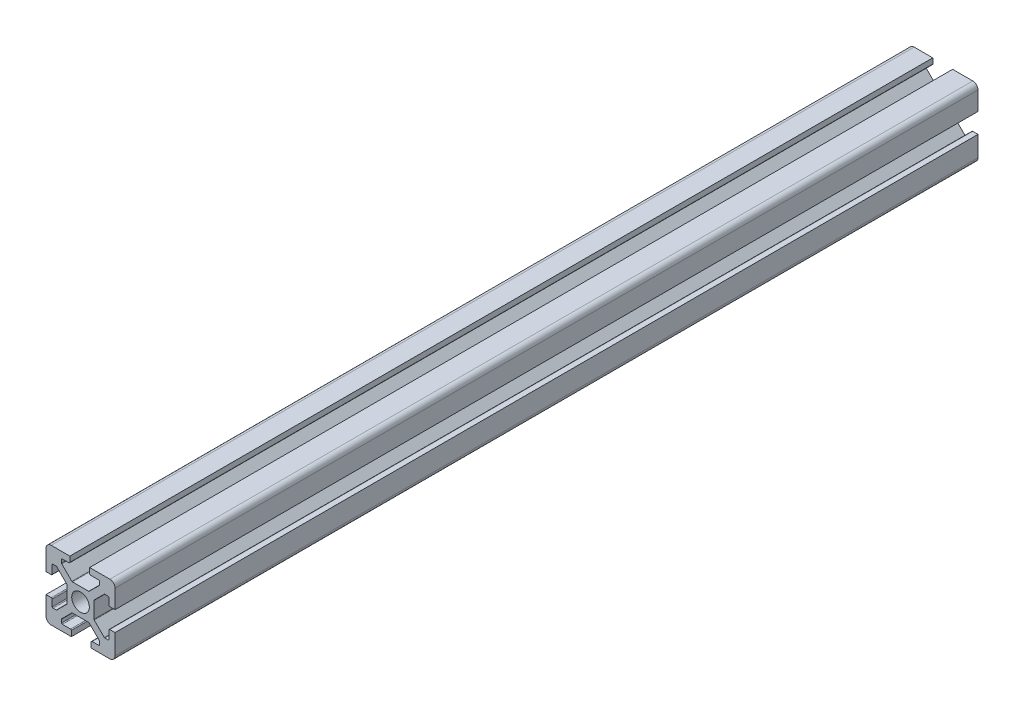
SolidWorks part; units mm, degrees
ref_plane "Front Plane" through (0, 0, 0) normal (0, 0, 1) x (1, 0, 0)
ref_plane "Top Plane" through (0, 0, 0) normal (0, 1, 0) x (1, 0, 0)
ref_plane "Right Plane" through (0, 0, 0) normal (1, 0, 0) x (0, 0, -1)
sketch "Sketch1" plane through (0, 0, 0) normal (0, 0, 1) x (1, 0, 0)
  line L1 (-8.5, -10) -> (-2.6476, -10)
  line L2 (-10, -8.5) -> (-10, -3.1)
  line L3 (-8.5, 10) -> (-3.1, 10)
  line L4 (10, -8.5) -> (10, -2.6476)
  line L5 (-1.8031, 1.8031) -> (1.8031, -1.8031) construction
  line L6 (-10, 10) -> (-3.9, 3.9) construction
  line L7 (2.3464, -3.9) -> (-2.3464, -3.9)
  line L8 (3.9, -2.3464) -> (3.9, 2.3464)
  line L9 (2.3464, 3.9) -> (-2.3464, 3.9)
  line L10 (-3.9, -2.3464) -> (-3.9, 2.3464)
  line L11 (1.8031, -1.8031) -> (-1.8031, 1.8031) construction
  line L12 (1.8031, 1.8031) -> (-1.8031, -1.8031) construction
  line L14 (-10, 2.6476) -> (-10, 8.5)
  line L15 (-10, 2.6476) -> (-8.45, 2.6476)
  line L17 (-10, -3.1) -> (-8.45, -3.1)
  line L18 (-3.9, 2.3464) -> (-3.9, -2.3464)
  line L19 (-8.2, 2.8976) -> (-8.2, 5.25)
  line L20 (-8.2, -3.35) -> (-8.2, -5.25)
  line L21 (-7.95, 5.5) -> (-7.0536, 5.5)
  line L22 (-6.8768, 5.4268) -> (-3.9732, 2.5232)
  line L23 (-6.8768, -5.4268) -> (-3.9732, -2.5232)
  line L24 (-7.95, -5.5) -> (-7.0536, -5.5)
  line L26 (-2.3464, 3.9) -> (2.3464, 3.9)
  line L27 (3.9, 3.9) -> (10, 10) construction
  line L28 (2.6476, 10) -> (2.6476, 8.45)
  line L29 (-3.1, 10) -> (-3.1, 8.45)
  line L30 (2.3464, 3.9) -> (-2.3464, 3.9)
  line L31 (2.8976, 8.2) -> (5.25, 8.2)
  line L32 (-3.35, 8.2) -> (-5.25, 8.2)
  line L33 (5.5, 7.95) -> (5.5, 7.0536)
  line L34 (5.4268, 6.8768) -> (2.5232, 3.9732)
  line L35 (-5.4268, 6.8768) -> (-2.5232, 3.9732)
  line L36 (-5.5, 7.95) -> (-5.5, 7.0536)
  line L37 (-1.8031, -1.8031) -> (1.8031, 1.8031) construction
  line L38 (3.9, 2.3464) -> (3.9, -2.3464)
  line L40 (10, -2.6476) -> (8.45, -2.6476)
  line L41 (10, 3.1) -> (8.45, 3.1)
  line L42 (3.9, -2.3464) -> (3.9, 2.3464)
  line L43 (8.2, -2.8976) -> (8.2, -5.25)
  line L44 (8.2, 3.35) -> (8.2, 5.25)
  line L45 (7.95, -5.5) -> (7.0536, -5.5)
  line L46 (6.8768, -5.4268) -> (3.9732, -2.5232)
  line L47 (6.8768, 5.4268) -> (3.9732, 2.5232)
  line L48 (7.95, 5.5) -> (7.0536, 5.5)
  line L50 (2.3464, -3.9) -> (-2.3464, -3.9)
  line L52 (-2.6476, -10) -> (-2.6476, -8.45)
  line L53 (3.1, -10) -> (3.1, -8.45)
  line L54 (-2.3464, -3.9) -> (2.3464, -3.9)
  line L55 (-2.8976, -8.2) -> (-5.25, -8.2)
  line L56 (3.35, -8.2) -> (5.25, -8.2)
  line L57 (-5.5, -7.95) -> (-5.5, -7.0536)
  line L58 (-5.4268, -6.8768) -> (-2.5232, -3.9732)
  line L59 (5.4268, -6.8768) -> (2.5232, -3.9732)
  line L60 (5.5, -7.95) -> (5.5, -7.0536)
  line L61 (2.6476, 10) -> (8.5, 10)
  line L62 (3.1, -10) -> (8.5, -10)
  line L63 (10, 3.1) -> (10, 8.5)
  line L65 (3.9, -3.9) -> (10, -10) construction
  circle A0 centre (0, 0) radius 2.55
  arc A1 (-8.2, -3.35) -> (-8.45, -3.1) centre (-8.45, -3.35) ccw
  arc A2 (-8.2, -5.25) -> (-7.95, -5.5) centre (-7.95, -5.25) ccw
  arc A3 (-6.8768, -5.4268) -> (-7.0536, -5.5) centre (-7.0536, -5.25) cw
  arc A4 (-3.9732, -2.5232) -> (-3.9, -2.3464) centre (-4.15, -2.3464) ccw
  arc A5 (-3.9, 2.3464) -> (-3.9732, 2.5232) centre (-4.15, 2.3464) ccw
  arc A6 (-7.0536, 5.5) -> (-6.8768, 5.4268) centre (-7.0536, 5.25) cw
  arc A7 (-8.2, 5.25) -> (-7.95, 5.5) centre (-7.95, 5.25) cw
  arc A8 (-8.2, 2.8976) -> (-8.45, 2.6476) centre (-8.45, 2.8976) cw
  arc A9 (-3.35, 8.2) -> (-3.1, 8.45) centre (-3.35, 8.45) ccw
  arc A10 (-5.25, 8.2) -> (-5.5, 7.95) centre (-5.25, 7.95) ccw
  arc A11 (-5.4268, 6.8768) -> (-5.5, 7.0536) centre (-5.25, 7.0536) cw
  arc A12 (-2.5232, 3.9732) -> (-2.3464, 3.9) centre (-2.3464, 4.15) ccw
  arc A13 (2.3464, 3.9) -> (2.5232, 3.9732) centre (2.3464, 4.15) ccw
  arc A14 (5.5, 7.0536) -> (5.4268, 6.8768) centre (5.25, 7.0536) cw
  arc A15 (5.25, 8.2) -> (5.5, 7.95) centre (5.25, 7.95) cw
  arc A16 (2.8976, 8.2) -> (2.6476, 8.45) centre (2.8976, 8.45) cw
  arc A17 (8.2, 3.35) -> (8.45, 3.1) centre (8.45, 3.35) ccw
  arc A18 (8.2, 5.25) -> (7.95, 5.5) centre (7.95, 5.25) ccw
  arc A19 (6.8768, 5.4268) -> (7.0536, 5.5) centre (7.0536, 5.25) cw
  arc A20 (3.9732, 2.5232) -> (3.9, 2.3464) centre (4.15, 2.3464) ccw
  arc A21 (3.9, -2.3464) -> (3.9732, -2.5232) centre (4.15, -2.3464) ccw
  arc A22 (7.0536, -5.5) -> (6.8768, -5.4268) centre (7.0536, -5.25) cw
  arc A23 (8.2, -5.25) -> (7.95, -5.5) centre (7.95, -5.25) cw
  arc A24 (8.2, -2.8976) -> (8.45, -2.6476) centre (8.45, -2.8976) cw
  arc A25 (3.35, -8.2) -> (3.1, -8.45) centre (3.35, -8.45) ccw
  arc A26 (5.25, -8.2) -> (5.5, -7.95) centre (5.25, -7.95) ccw
  arc A27 (5.4268, -6.8768) -> (5.5, -7.0536) centre (5.25, -7.0536) cw
  arc A28 (2.5232, -3.9732) -> (2.3464, -3.9) centre (2.3464, -4.15) ccw
  arc A29 (-2.3464, -3.9) -> (-2.5232, -3.9732) centre (-2.3464, -4.15) ccw
  arc A30 (-5.5, -7.0536) -> (-5.4268, -6.8768) centre (-5.25, -7.0536) cw
  arc A31 (-5.25, -8.2) -> (-5.5, -7.95) centre (-5.25, -7.95) cw
  arc A32 (-2.8976, -8.2) -> (-2.6476, -8.45) centre (-2.8976, -8.45) cw
  arc A33 (-10, -8.5) -> (-8.5, -10) centre (-8.5, -8.5) ccw
  arc A34 (8.5, -10) -> (10, -8.5) centre (8.5, -8.5) ccw
  arc A35 (10, 8.5) -> (8.5, 10) centre (8.5, 8.5) ccw
  arc A36 (-10, 8.5) -> (-8.5, 10) centre (-8.5, 8.5) cw
  point P15 (-10, -10)
  point P131 (0, 0)
  dimension "D1" = 20
  dimension "D4" = 5.1
  dimension "D5" = 0.25
  dimension "D6" = 1.5
  dimension "D2" = 20
  dimension "D3" = 4
extrude "Boss-Extrude1" add sketch "Sketch1" along normal blind 250 contours A36 L14 L15 A8 L19 A7 L21 A6 L22 A5 L10 A4 L23 A3 L24 A2 L20 A1 L17 L2 A33 L1 L52 A32 L55 A31 L57 A30 L58 A29 L7 A28 L59 A27 L60 A26 L56 A25 L53 L62 A34 L4 L40 A24 L43 A23 L45 A22 L46 A21 L8
